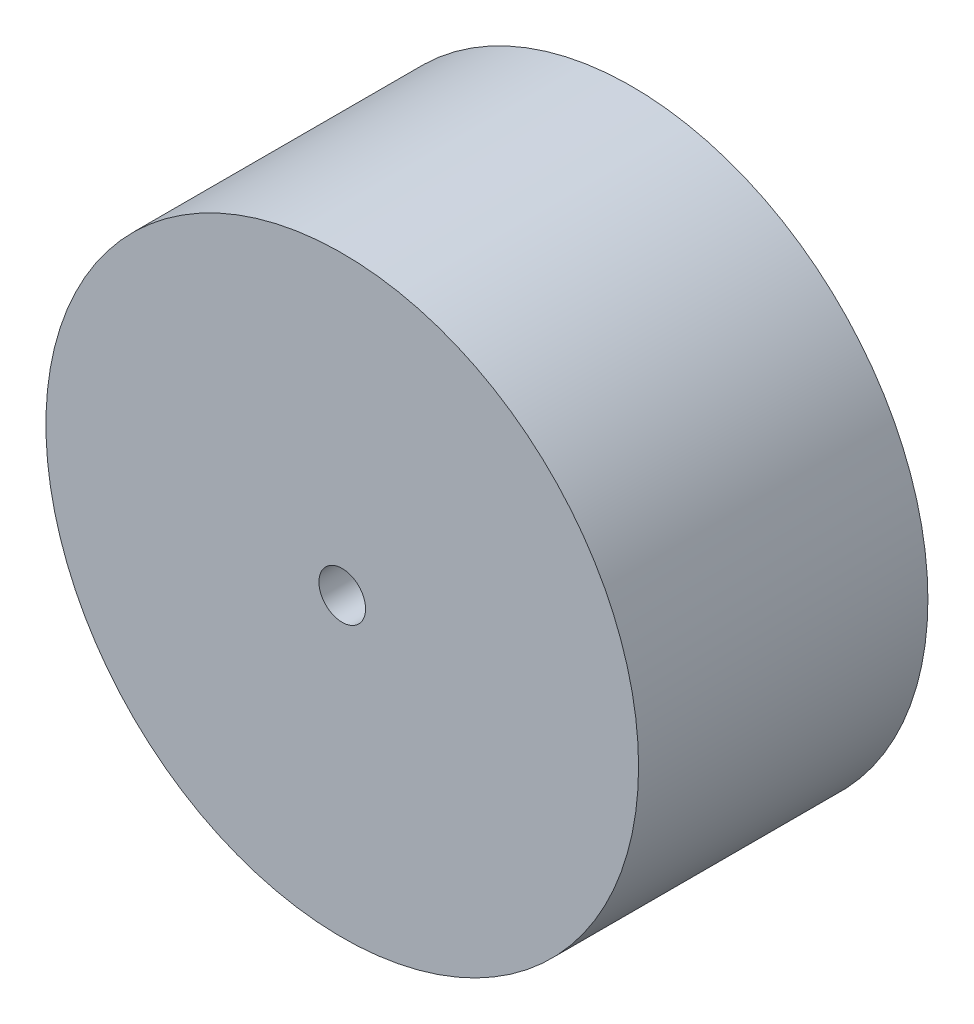
SolidWorks part; units mm, degrees
ref_plane "Front Plane" through (0, 0, 0) normal (0, 0, 1) x (1, 0, 0)
ref_plane "Top Plane" through (0, 0, 0) normal (0, 1, 0) x (1, 0, 0)
ref_plane "Right Plane" through (0, 0, 0) normal (1, 0, 0) x (0, 0, -1)
sketch "Sketch1" plane through (0, 0, 0) normal (0, 0, 1) x (1, 0, 0)
  circle A0 centre (0, 0) radius 63.5
  dimension "D1" = 127
extrude "Boss-Extrude1" add sketch "Sketch1" along normal blind 62
sketch "Sketch2" plane through (0, 0, 0) normal (0, 0, -1) x (-1, 0, 0)
  circle A1 centre (0, 0) radius 5
extrude "Cut-Extrude1" cut sketch "Sketch2" against normal through all
